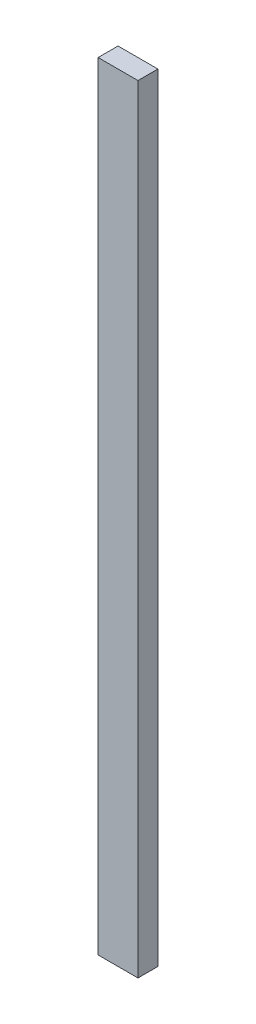
SolidWorks part; units mm, degrees
ref_plane "Спереди" through (0, 0, 0) normal (0, 0, 1) x (1, 0, 0)
ref_plane "Сверху" through (0, 0, 0) normal (0, 1, 0) x (1, 0, 0)
ref_plane "Справа" through (0, 0, 0) normal (1, 0, 0) x (0, 0, -1)
sketch "Эскиз1" plane through (0, 0, 0) normal (0, 1, 0) x (1, 0, 0)
  line L1 (0, 0) -> (40, 0)
  line L2 (0, 0) -> (0, 20)
  line L3 (0, 20) -> (40, 20)
  line L4 (40, 0) -> (40, 20)
extrude "Бобышка-Вытянуть1" add sketch "Эскиз1" along normal blind 780
